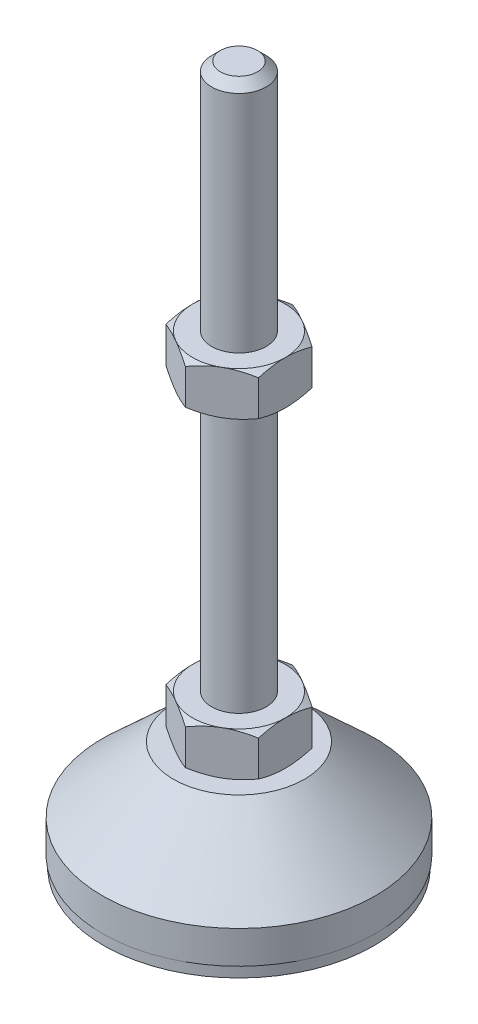
SolidWorks part; units mm, degrees
ref_plane "Спереди" through (0, 0, 0) normal (0, 0, 1) x (1, 0, 0)
ref_plane "Сверху" through (0, 0, 0) normal (0, 1, 0) x (1, 0, 0)
ref_plane "Справа" through (0, 0, 0) normal (1, 0, 0) x (0, 0, -1)
sketch "Эскиз1" plane through (0, 0, 0) normal (0, 0, 1) x (1, 0, 0)
  line L0 (0, 0) -> (-24.8, 0)
  line L1 (-24.8, 0) -> (-24.8, 2)
  line L2 (-24.8, 2) -> (-25, 2)
  line L3 (-25, 2) -> (-25, 8)
  line L4 (-25, 8) -> (-12, 20)
  line L5 (-12, 20) -> (-5, 20)
  line L12 (-5, 28) -> (-5, 126.4)
  line L13 (-5, 126.4) -> (-3.4, 128)
  line L14 (-3.4, 128) -> (0, 128)
  line L15 (0, 128) -> (0, 0) construction
  line L16 (-5, 20) -> (0, 20) construction
  line L17 (0, 0) -> (0, 128)
  line L18 (0, 0) -> (0, -7.9595) construction
  line L19 (-5, 28) -> (-5, 20)
  point P8 (-5, 77.2)
  point P23 (-8.5, 20)
  dimension "D1" = 10
  dimension "D2" = 20
  dimension "D3" = 8
  dimension "D4" = 50
  dimension "D5" = 5
  dimension "D6" = 1.6
  dimension "D7" = 45
  dimension "D8" = 24
  dimension "D9" = 2
  dimension "D10" = 100
  dimension "D11" = 6
  dimension "D12" = 0.2
revolve "Повернуть1" add sketch "Эскиз1" angle 360 about L17
sketch "Эскиз2" plane through (0, 20, 0) normal (0, 1, 0) x (1, 0, 0)
  line L1 (0, 9.815) -> (-8.5, 4.9075)
  line L2 (-8.5, 4.9075) -> (-8.5, -4.9075)
  line L3 (-8.5, -4.9075) -> (0, -9.815)
  line L4 (0, -9.815) -> (8.5, -4.9075)
  line L5 (8.5, -4.9075) -> (8.5, 4.9075)
  line L6 (8.5, 4.9075) -> (0, 9.815)
  circle A0 centre (0, 0) radius 8.5 construction
  dimension "D1" = 17
extrude "Бобышка-Вытянуть1" add sketch "Эскиз2" along normal up to vertex (8 mm away) up to point (-5, 28, 0)
ref_plane "Плоскость1" through (0, 77.2, 0) normal (0, 1, 0) x (1, 0, 0)
sketch "Эскиз3" plane through (0, 77.2, 0) normal (0, 1, 0) x (1, 0, 0)
  line L6 (8.5, 4.9075) -> (0, 9.815)
  line L7 (0, 9.815) -> (-8.5, 4.9075)
  line L8 (-8.5, 4.9075) -> (-8.5, -4.9075)
  line L9 (-8.5, -4.9075) -> (0, -9.815)
  line L10 (0, -9.815) -> (8.5, -4.9075)
  line L11 (8.5, -4.9075) -> (8.5, 4.9075)
  line L12 (8.5, 4.9075) -> (0, 9.815)
  line L13 (0, 9.815) -> (-8.5, 4.9075)
  line L14 (-8.5, 4.9075) -> (-8.5, -4.9075)
  line L15 (-8.5, -4.9075) -> (0, -9.815)
  line L16 (0, -9.815) -> (8.5, -4.9075)
  line L17 (8.5, -4.9075) -> (8.5, 4.9075)
  dimension "D1" = 0
extrude "Бобышка-Вытянуть2" add sketch "Эскиз3" along normal blind 8
sketch "Эскиз4" plane through (0, 0, 0) normal (0, 0, 1) x (1, 0, 0)
  line L0 (-8.5, 85.2) -> (-15.4282, 81.2)
  line L1 (-15.4282, 81.2) -> (-15.4282, 85.2)
  line L2 (-15.4282, 85.2) -> (-8.5, 85.2)
  line L3 (-15.4282, 81.2) -> (-8.5, 77.2)
  line L4 (50, 77.2) -> (-50, 77.2) construction
  line L5 (-8.5, 77.2) -> (-15.4282, 77.2)
  line L6 (-15.4282, 77.2) -> (-15.4282, 81.2)
  line L7 (-8.5, 85.2) -> (-8.5, 77.2) construction
  line L8 (-8.5, 28) -> (-15.4282, 28)
  line L9 (-15.4282, 28) -> (-15.4282, 24)
  line L10 (-15.4282, 24) -> (-8.5, 28)
  line L11 (-8.5, 20) -> (-15.4282, 24)
  line L12 (-15.4282, 24) -> (-15.4282, 20)
  line L13 (-15.4282, 20) -> (-8.5, 20)
  line L14 (0, 128) -> (0, 96.3793) construction
  dimension "D1" = 30
  dimension "D2" = 30
revolve "Вырез-Повернуть2" cut sketch "Эскиз4" angle 360 about L14
